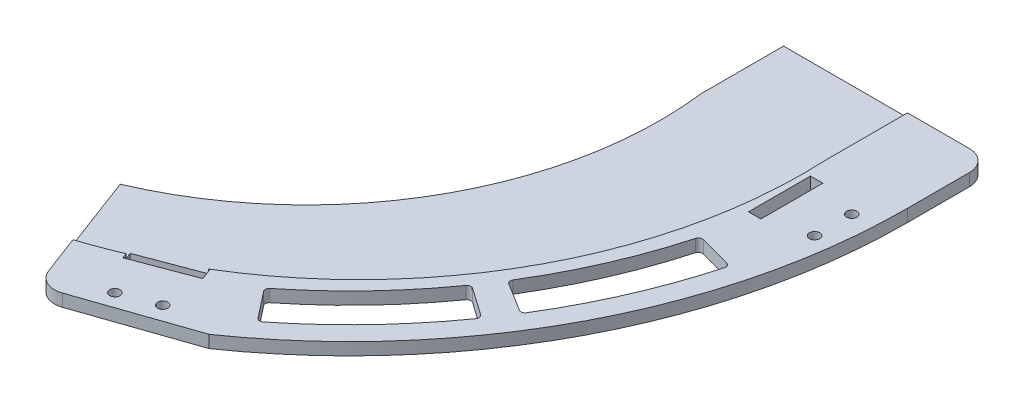
SolidWorks part; units mm, degrees
ref_plane "前视基准面" through (0, 0, 0) normal (0, 0, 1) x (1, 0, 0)
ref_plane "上视基准面" through (0, 0, 0) normal (0, 1, 0) x (1, 0, 0)
ref_plane "右视基准面" through (0, 0, 0) normal (1, 0, 0) x (0, 0, -1)
other "Configuration Table"
sketch "草图4" plane through (0, 0, 0) normal (0, 1, 0) x (1, 0, 0)
  line L0 (0, 0) -> (135, 0)
  line L1 (0, 0) -> (0, -135)
  arc A0 (0, -135) -> (135, 0) centre (0, 0) ccw
  dimension "D1" = 135
extrude "凸台-拉伸2" add sketch "草图4" along normal blind 3
sketch "草图6" plane through (0, 3, 0) normal (0, 1, 0) x (1, 0, 0)
  line L0 (0, 0) -> (85, 0)
  line L1 (0, 0) -> (0, -18)
  line L2 (0, -79.5299) -> (30, -79.5299) construction
  line L3 (0, 0) -> (30, -79.5299) construction
  line L4 (30, -79.5299) -> (47.6471, -126.3121)
  line L5 (0, -18) -> (0, -135)
  arc A0 (30, -79.5299) -> (85, 0) centre (0, 0) ccw
  arc A1 (0, -135) -> (135, 0) centre (0, 0) ccw construction
  arc A2 (0, -135) -> (47.6471, -126.3121) centre (0, 0) ccw
  dimension "D1" = 85
  dimension "D2" = 30
extrude "切除-拉伸1" cut sketch "草图6" against normal blind 3
sketch "草图8" plane through (0, 3, 0) normal (0, 1, 0) x (1, 0, 0)
  line L0 (45.8824, -121.6339) -> (76.9087, -110.9507)
  line L1 (45.8824, -121.6339) -> (90.3547, -121.6339) construction
  line L4 (47.6471, -126.3121) -> (30, -79.5299) construction
  line L5 (45.8824, -121.6339) -> (47.6471, -126.3121)
  arc A2 (47.6471, -126.3121) -> (135, 0) centre (0, 0) ccw construction
  arc A3 (47.6471, -126.3121) -> (76.9087, -110.9507) centre (0, 0) ccw
  dimension "D1" = 5
  dimension "D2" = 19
extrude "切除-拉伸2" cut sketch "草图8" against normal blind 3
sketch "草图9" plane through (0, 3, 0) normal (0, 1, 0) x (1, 0, 0)
  line L1 (135, 0) -> (85, 0) construction
  line L5 (40.5882, -107.5992) -> (30, -79.5299)
  line L6 (85, 0) -> (115, 0)
  line L9 (45.8824, -121.6339) -> (30, -79.5299) construction
  arc A2 (30, -79.5299) -> (85, 0) centre (0, 0) ccw
  arc A3 (40.5882, -107.5992) -> (115, 0) centre (7.6296, -5.2763) ccw
  dimension "D1" = 107.5
  dimension "D2" = 15
  dimension "D3" = 30
extrude "切除-拉伸3" cut sketch "草图9" against normal blind 1
sketch "草图16" plane through (0, 2, 0) normal (0, 1, 0) x (1, 0, 0)
  line L0 (30, -79.5299) -> (40.5882, -107.5992) construction
  line L1 (40.5882, -107.5992) -> (33.6671, -89.2514) construction
  line L2 (0, 0) -> (0, -100.9465) construction
  circle A0 centre (0, -10.5) radius 85.6461
  dimension "D1" = 10.5
extrude "切除-拉伸6" cut sketch "草图16" against normal blind 10
ref_plane "基准面1" through (0, 0, 10.5) normal (0, 0, 1) x (1, 0, 0)
sketch "草图13" plane through (0, 0, 0) normal (0, 0, -1) x (-1, 0, 0)
  line L0 (-135, 3) -> (-135, 0)
  line L4 (-115, 2) -> (-115, 3)
  line L5 (-115, 3) -> (-135, 3)
  line L10 (-115, 2) -> (-85, 2)
  line L11 (-85, 2) -> (-85, 0)
  line L12 (-85, 0) -> (-135, 0)
extrude "凸台-拉伸3" add sketch "草图13" along normal blind 20
fillet "圆角1" radius 5 2 edges at (45.8824, 1.5, 121.6339) (135, 1.5, -20)
sketch "草图14" plane through (0, 3, 0) normal (0, 1, 0) x (1, 0, 0)
  line L0 (69.2247, -112.6809) -> (55.19, -117.9751) construction
  line L1 (116.5, -12.5) -> (134.5, -12.5) construction
  line L2 (116.5, -5) -> (119.5, -5)
  line L3 (116.5, -5) -> (116.5, -20)
  line L4 (116.5, -20) -> (119.5, -20)
  line L5 (119.5, -5) -> (119.5, -20)
  line L6 (55.19, -117.9751) -> (50.4253, -105.3438) construction
  line L7 (50.4253, -105.3438) -> (64.46, -100.0497) construction
  line L8 (119.5, -5) -> (134.5, -5) construction
  line L9 (119.5, -5) -> (119.5, -20) construction
  line L10 (119.5, -20) -> (134.5, -20) construction
  line L11 (134.5, -5) -> (134.5, -20) construction
  line L12 (64.46, -100.0497) -> (69.2247, -112.6809) construction
  line L17 (50.4253, -105.3438) -> (49.3664, -102.5369)
  line L22 (115, 20) -> (130, 20) construction
  line L23 (49.3664, -102.5369) -> (63.4011, -97.2428)
  line L24 (63.4011, -97.2428) -> (64.46, -100.0497)
  line L25 (56.7616, -113.6415) -> (65.1824, -110.465) construction
  line L26 (50.4253, -105.3438) -> (64.46, -100.0497)
  line L27 (56.3838, -99.8898) -> (57.4426, -102.6968) construction
  line L28 (44.1683, -117.0899) -> (40.5882, -107.5992) construction
  line L31 (115, 20) -> (115, 0) construction
  circle A3 centre (129.5, -17) radius 1.25
  circle A4 centre (129.5, -8) radius 1.25
  circle A5 centre (56.7616, -113.6415) radius 1.25
  circle A6 centre (65.1824, -110.465) radius 1.25
  dimension "D2" = 2.5
  dimension "D3" = 2.5
  dimension "D14" = 9
  dimension "D15" = 2.5
  dimension "D16" = 2.5
  dimension "D4" = 9
  dimension "D5" = 25
  dimension "D6" = 10
  dimension "D7" = 15
  dimension "D8" = 4.5
  dimension "D9" = 3
  dimension "D10" = 15
  dimension "D11" = 15
  dimension "D12" = 10
  dimension "D13" = 16.5
  dimension "D17" = 4.5
  dimension "D18" = 10
  dimension "D19" = 8.7782
  dimension "D20" = 1.5
  dimension "D21" = 10
  dimension "D22" = 3
extrude "切除-拉伸8" cut sketch "草图14" against normal blind 10
sketch "草图17" plane through (0, 3, 0) normal (0, 1, 0) x (1, 0, 0)
  line L0 (115.9111, -31.0583) -> (125.5704, -33.6465)
  line L1 (73.8794, -94.5613) -> (80.036, -102.4414)
  line L3 (0, 0) -> (115.9111, -31.0583) construction
  line L4 (0, 0) -> (73.8794, -94.5613) construction
  line L5 (0, 0) -> (98.2982, -68.8292) construction
  line L6 (98.2982, -68.8292) -> (0, 0) construction
  line L7 (0, 0) -> (101.7658, -63.5903) construction
  line L8 (0, 0) -> (135, 0) construction
  line L9 (98.2982, -68.8292) -> (106.4898, -74.5649)
  line L10 (101.7658, -63.5903) -> (110.2463, -68.8895)
  circle A0 centre (0, 0) radius 135 construction
  arc A1 (80.036, -102.4414) -> (106.4898, -74.5649) centre (0, 0) ccw
  arc A2 (73.8794, -94.5613) -> (98.2982, -68.8292) centre (0, 0) ccw
  arc A3 (101.7658, -63.5903) -> (115.9111, -31.0583) centre (0, 0) ccw
  arc A4 (110.2463, -68.8895) -> (125.5704, -33.6465) centre (0, 0) ccw
  dimension "D1" = 270
  dimension "D2" = 130
  dimension "D3" = 120
  dimension "D4" = 15
  dimension "D5" = 3
  dimension "D6" = 17
  dimension "D7" = 17
extrude "切除-拉伸9" cut sketch "草图17" against normal blind 10
fillet "圆角2" radius 1 8 edges at (80.036, 1.5, 102.4414) (73.8794, 1.5, 94.5613) (101.7658, 1.5, 63.5903) (110.2463, 1.5, 68.8895) (98.2982, 1.5, 68.8292) (106.4898, 1.5, 74.5649) (125.5704, 1.5, 33.6465) (115.9111, 1.5, 31.0583)
